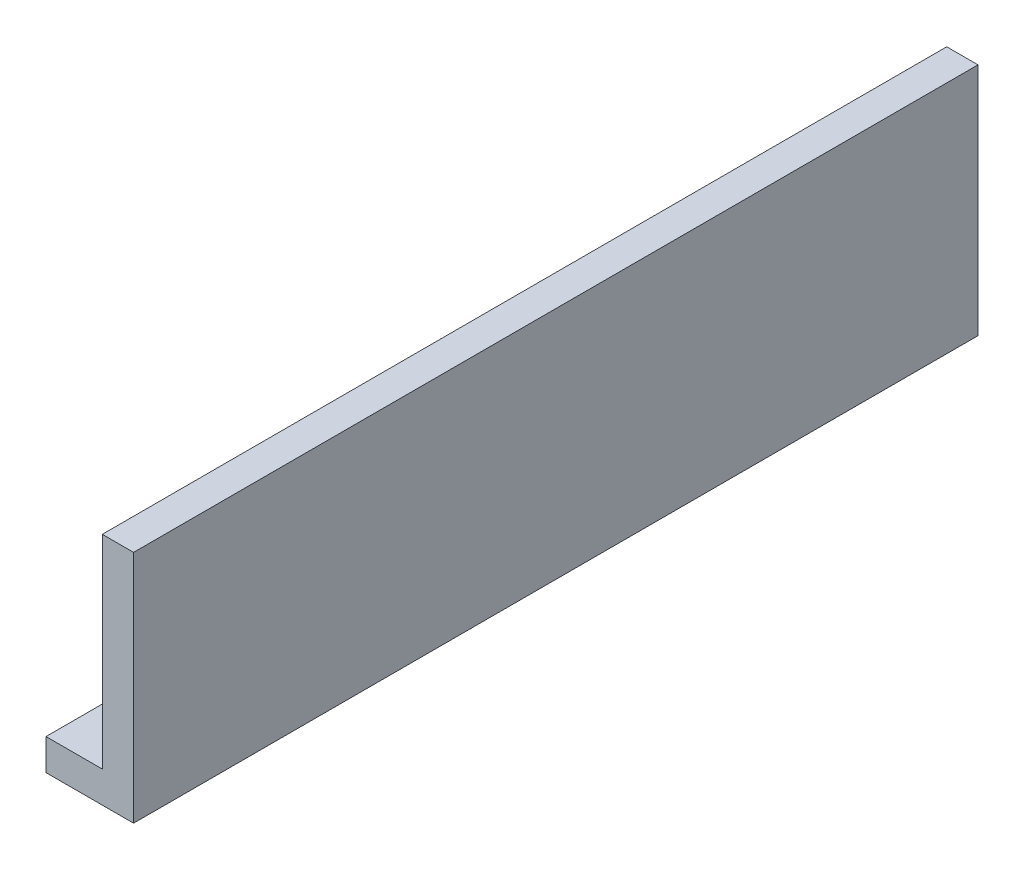
SolidWorks part; units mm, degrees
ref_plane "Front Plane" through (0, 0, 0) normal (0, 0, 1) x (1, 0, 0)
ref_plane "Top Plane" through (0, 0, 0) normal (0, 1, 0) x (1, 0, 0)
ref_plane "Right Plane" through (0, 0, 0) normal (1, 0, 0) x (0, 0, -1)
sketch "Sketch1" plane through (0, 0, 0) normal (0, 1, 0) x (1, 0, 0)
  line L1 (0, 270) -> (20, 270)
  line L2 (0, 270) -> (0, -270)
  line L3 (0, -270) -> (20, -270)
  line L4 (20, 270) -> (20, -270)
  dimension "D1" = 20
  dimension "D2" = 540
extrude "Boss-Extrude1" add sketch "Sketch1" along normal blind 150
sketch "Sketch2" plane through (0, 0, 0) normal (1, 0, 0) x (0, 0, -1)
  line L0 (270, 150) -> (270, 0) construction
  line L2 (270, 20) -> (-270, 20)
  line L3 (270, 20) -> (270, 0)
  line L4 (270, 0) -> (-270, 0)
  line L5 (-270, 20) -> (-270, 0)
  dimension "D1" = 20
extrude "Boss-Extrude2" add sketch "Sketch2" against normal blind 36
sketch "Sketch3" plane through (0, 150, 0) normal (0, 1, 0) x (1, 0, 0)
  line L0 (0, 270) -> (0, -270) construction
  point P0 (-16, 80)
  point P1 (-16, 160)
  point P2 (-16, 240)
  dimension "D1" = 80
  dimension "D2" = 80
  dimension "D3" = 80
  dimension "D4" = 16
hole_wizard "M10 Tapped Hole1" positions "3DSketch1" profile "Sketch4" tap size "M10" standard "ISO" end condition through all
sketch3d "3DSketch1"
  point P0 (-16, 150, -240)
  point P3 (-16, 150, -160)
  point P6 (-16, 150, -80)
sketch "Sketch4" plane through (-16, 150, -240) normal (1, 0, 0) x (0, 0, 1)
  line L0 (0, 0) -> (0, 150)
  line L1 (0, 150) -> (4.25, 150)
  line L2 (4.25, 150) -> (4.25, 0)
  line L5 (4.25, 0) -> (0, 0)
  line L11 (0, -6.35) -> (0, 107.95) construction
  dimension "Thru Tap Drill Dia." = 8.5
  dimension "Thru Tap Drill Depth" = 150
cosmetic thread "Hole Thread1" parameters "D2"=10
cosmetic thread "Hole Thread2" parameters "D2"=10
cosmetic thread "Hole Thread3" parameters "D2"=10
mirror "Mirror1" about plane through (0, 0, 0) normal (0, 0, 1) of "M10 Tapped Hole1"
cosmetic thread "Hole Thread4" parameters "D2"=10
cosmetic thread "Hole Thread5" parameters "D2"=10
cosmetic thread "Hole Thread6" parameters "D2"=10
